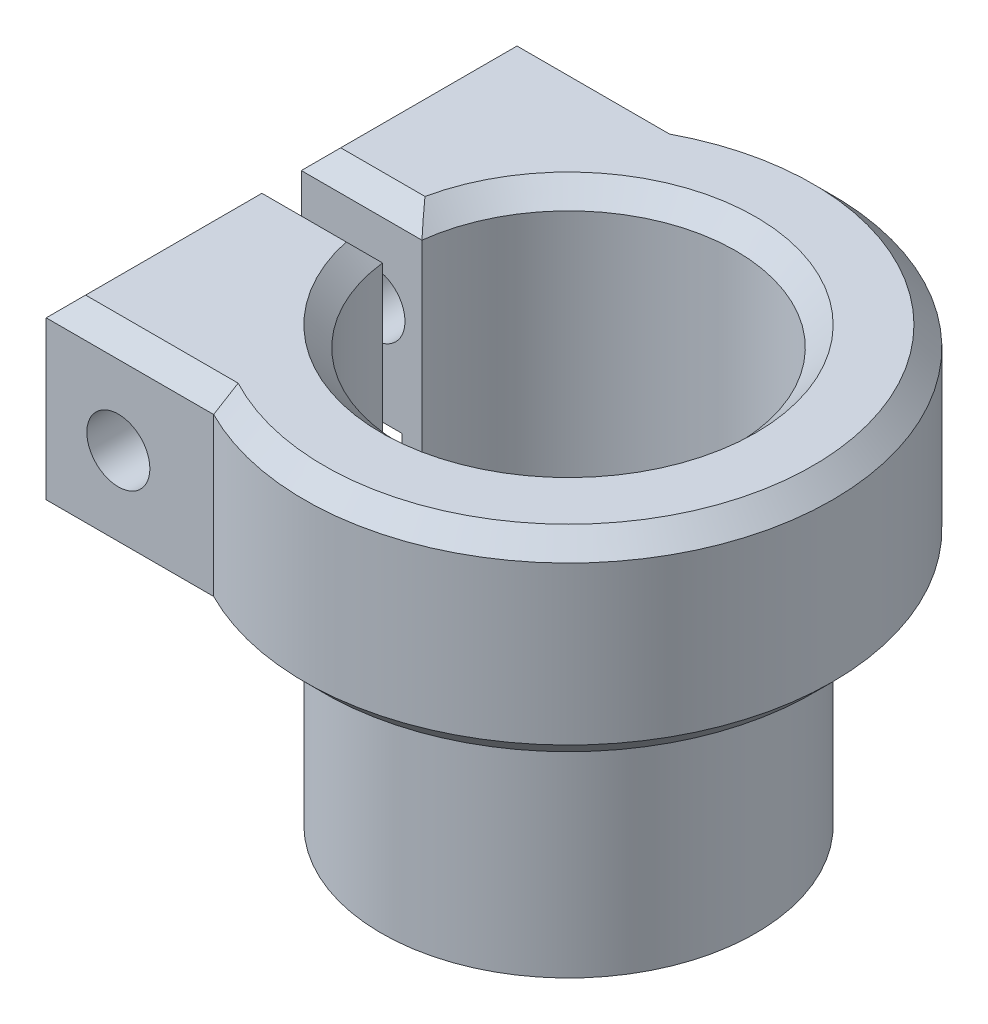
SolidWorks part; units mm, degrees
ref_plane "Front Plane" through (0, 0, 0) normal (0, 0, 1) x (1, 0, 0)
ref_plane "Top Plane" through (0, 0, 0) normal (0, 1, 0) x (1, 0, 0)
ref_plane "Right Plane" through (0, 0, 0) normal (1, 0, 0) x (0, 0, -1)
sketch "Sketch1" plane through (0, 0, 0) normal (0, 1, 0) x (1, 0, 0)
  circle A0 centre (0, 0) radius 8.5
  circle A1 centre (0, 0) radius 9.5
  dimension "D1" = 19
  dimension "D2" = 17
extrude "Boss-Extrude1" add sketch "Sketch1" along normal blind 12
sketch "Sketch2" plane through (0, 12, 0) normal (0, 1, 0) x (1, 0, 0)
  circle A0 centre (0, 0) radius 8.5
  circle A1 centre (0, 0) radius 13.4
  dimension "D1" = 26.8
extrude "Boss-Extrude2" add sketch "Sketch2" along normal blind 10
sketch "Sketch3" plane through (0, 0, 0) normal (1, 0, 0) x (0, 0, -1)
  line L0 (0, 0) -> (0, 22) construction
  line L1 (8.5, 22) -> (-8.5, 22) construction
  line L2 (13.4, 22) -> (-13.4, 22) construction
  line L3 (-1, 22) -> (1, 22)
  line L4 (-1, 22) -> (-1, 0)
  line L5 (-1, 0) -> (1, 0)
  line L6 (1, 22) -> (1, 0)
  line L7 (-9.5, 0) -> (9.5, 0) construction
  dimension "D1" = 2
extrude "Cut-Extrude1" cut sketch "Sketch3" against normal blind 21
sketch "Sketch6" plane through (0, 22, 0) normal (0, 1, 0) x (1, 0, 0)
  line L0 (0, 0) -> (-15.7617, 0) construction
  line L1 (-9.5183, -1) -> (-14.5637, -1)
  line L2 (-9.5183, -1) -> (-6.0637, -11.9495)
  line L3 (-6.0637, -11.9495) -> (-14.5637, -11.9495)
  line L4 (-14.5637, -1) -> (-14.5637, -11.9495)
  line L5 (-6.0637, 11.9495) -> (-14.5637, 11.9495)
  line L6 (-14.5637, 1) -> (-14.5637, 11.9495)
  line L7 (-9.5183, 1) -> (-14.5637, 1)
  line L8 (-9.5183, 1) -> (-6.0637, 11.9495)
  line L9 (-13.3626, -1) -> (-8.441, -1) construction
  arc A0 (-13.3626, -1) -> (-13.3626, 1) centre (0, 0) ccw construction
  point P16 (0, 0)
  point P17 (0, 0)
  point P18 (-9.5183, -1)
  point P21 (0, 0)
  point P22 (0, 0)
  dimension "D1" = 8.5
extrude "Boss-Extrude3" add sketch "Sketch6" against normal blind 10
sketch "Sketch4" plane through (0, 0, -1) normal (0, 0, 1) x (1, 0, 0)
  line L6 (-8.441, 22) -> (-14.5637, 12) construction
  circle A1 centre (-10.9018, 17) radius 1.6
  dimension "D1" = 3.2
extrude "Cut-Extrude2" cut sketch "Sketch4" against normal blind 21 and the other way blind 21
chamfer "Chamfer1" distance 1 angle 45 13 edges at (-10.3137, 22, 11.9495) (-14.5637, 22, 6.4748) (-11.5023, 22, 1) (8.5, 22, 0) (-11.5023, 22, -1) (-14.5637, 22, -6.4748) (-10.3137, 22, -11.9495) (13.4, 12, 0) (13.4, 22, 0) (-14.5637, 12, -6.4748) (-14.5637, 12, 6.4748) (-10.3137, 12, 11.9495) (-10.3137, 12, -11.9495)
